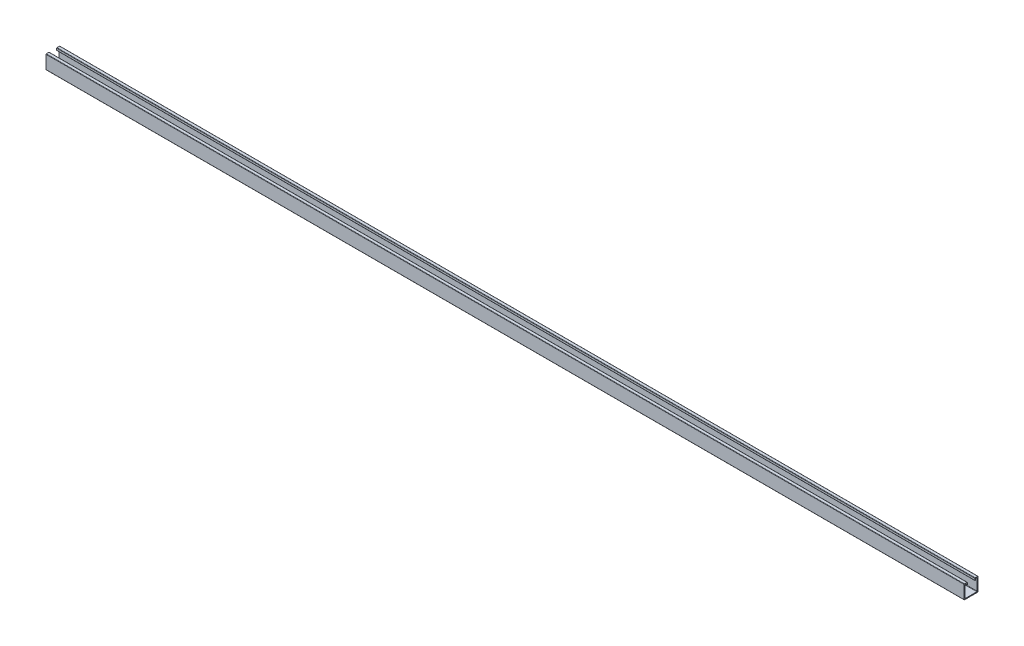
SolidWorks part; units mm, degrees
material "Alloy Steel (SS)"
ref_plane "Front Plane" through (0, 0, 0) normal (0, 0, 1) x (1, 0, 0)
ref_plane "Top Plane" through (0, 0, 0) normal (0, 1, 0) x (1, 0, 0)
ref_plane "Right Plane" through (0, 0, 0) normal (1, 0, 0) x (0, 0, -1)
sketch "Sketch1" plane through (0, 0, 0) normal (1, 0, 0) x (0, 0, -1)
  line L12 (-18, -17) -> (-18, 17)
  line L13 (-19.5, -20.5) -> (19.5, -20.5)
  line L14 (-20.5, -19.5) -> (-20.5, 19.5)
  line L15 (-19.5, 20.5) -> (-12, 20.5)
  line L16 (20.5, -19.5) -> (20.5, 19.5)
  line L17 (-20.5, -20.5) -> (20.5, 20.5) construction
  line L18 (-20.5, 20.5) -> (20.5, -20.5) construction
  line L19 (-17, 18) -> (-14.5, 18)
  line L20 (18, -17) -> (18, 17)
  line L21 (-17, -18) -> (17, -18)
  line L22 (11, 19.5) -> (11, 14.4)
  line L23 (12, 13.4) -> (12.5, 13.4)
  line L24 (13.5, 14.4) -> (13.5, 17)
  line L25 (-11, 19.5) -> (-11, 14.4)
  line L26 (-12, 13.4) -> (-12.5, 13.4)
  line L27 (-13.5, 17) -> (-13.5, 14.4)
  line L28 (14.5, 18) -> (17, 18)
  line L29 (-18, 18) -> (18, 18) construction
  line L30 (20.5, -20.5) -> (20.5, 20.5) construction
  line L31 (12, 20.5) -> (19.5, 20.5)
  line L32 (-20.5, 20.5) -> (20.5, 20.5) construction
  line L33 (18, -18) -> (18, 18) construction
  line L34 (-18, -18) -> (-18, 18) construction
  line L35 (-20.5, -20.5) -> (-20.5, 20.5) construction
  line L36 (-18, -18) -> (18, -18) construction
  line L37 (-20.5, -20.5) -> (20.5, -20.5) construction
  arc A0 (20.5, 19.5) -> (19.5, 20.5) centre (19.5, 19.5) ccw
  arc A1 (18, 17) -> (17, 18) centre (17, 17) ccw
  arc A2 (13.5, 17) -> (14.5, 18) centre (14.5, 17) cw
  arc A3 (12, 20.5) -> (11, 19.5) centre (12, 19.5) ccw
  arc A4 (12.5, 13.4) -> (13.5, 14.4) centre (12.5, 14.4) ccw
  arc A5 (12, 13.4) -> (11, 14.4) centre (12, 14.4) cw
  arc A6 (-12.5, 13.4) -> (-13.5, 14.4) centre (-12.5, 14.4) cw
  arc A7 (-12, 13.4) -> (-11, 14.4) centre (-12, 14.4) ccw
  arc A8 (-11, 19.5) -> (-12, 20.5) centre (-12, 19.5) ccw
  arc A9 (-14.5, 18) -> (-13.5, 17) centre (-14.5, 17) cw
  arc A10 (-17, 18) -> (-18, 17) centre (-17, 17) ccw
  arc A11 (-19.5, 20.5) -> (-20.5, 19.5) centre (-19.5, 19.5) ccw
  arc A12 (-17, -18) -> (-18, -17) centre (-17, -17) cw
  arc A13 (-20.5, -19.5) -> (-19.5, -20.5) centre (-19.5, -19.5) ccw
  arc A14 (20.5, -19.5) -> (19.5, -20.5) centre (19.5, -19.5) cw
  arc A15 (18, -17) -> (17, -18) centre (17, -17) cw
  point P0 (0, 0)
  point P25 (13.5, 18)
  point P28 (11, 20.5)
  dimension "D8" = 7.1
  dimension "D9" = 1
  dimension "D1" = 41
  dimension "D2" = 41
  dimension "D3" = 2.5
  dimension "D4" = 9.5
  dimension "D5" = 9.5
  dimension "D6" = 2.5
  dimension "D7" = 2.5
extrude "Boss-Extrude1" add sketch "Sketch1" along normal blind 2717.8
